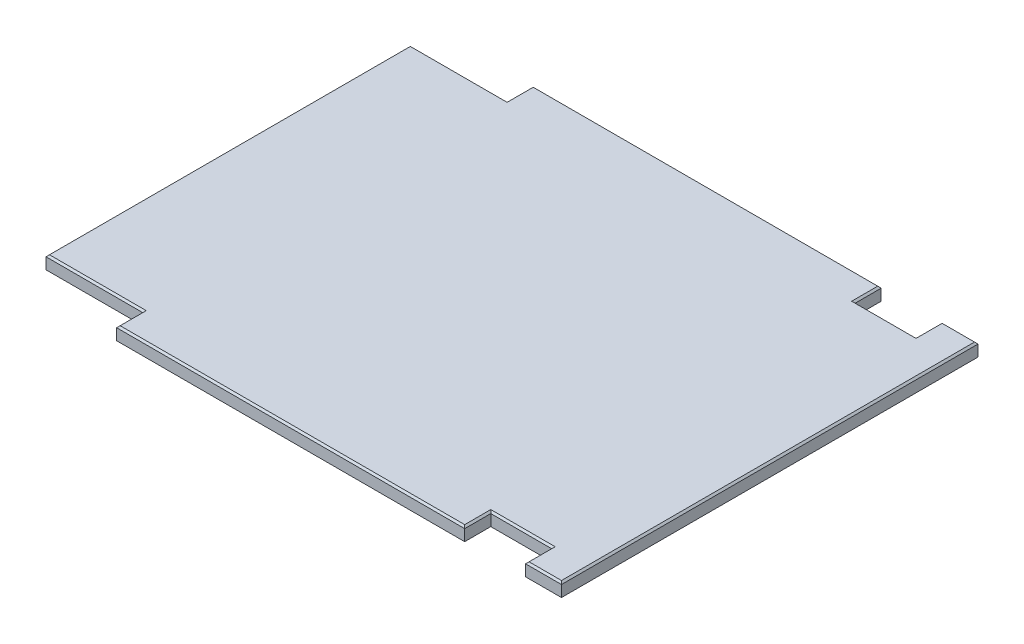
SolidWorks part; units mm, degrees
material "Oak"
ref_plane "Front Plane" through (0, 0, 0) normal (0, 0, 1) x (1, 0, 0)
ref_plane "Top Plane" through (0, 0, 0) normal (0, 1, 0) x (1, 0, 0)
ref_plane "Right Plane" through (0, 0, 0) normal (1, 0, 0) x (0, 0, -1)
sketch "Sketch1" plane through (0, 0, 0) normal (0, 1, 0) x (1, 0, 0)
  line L1 (0, 0) -> (790.575, 0)
  line L2 (0, 0) -> (0, 608.0125)
  line L3 (0, 608.0125) -> (790.575, 608.0125)
  line L4 (790.575, 0) -> (790.575, 608.0125)
  dimension "D1" = 608.0125
  dimension "D2" = 790.575
extrude "Boss-Extrude1" add sketch "Sketch1" along normal blind 19.05
sketch "Sketch2" plane through (0, 19.05, 0) normal (0, 1, 0) x (1, 0, 0)
  line L0 (-127.9594, 304.0062) -> (1156.0653, 304.0062) construction
  line L1 (738.1875, 569.9125) -> (649.2875, 569.9125)
  line L2 (738.1875, 569.9125) -> (738.1875, 608.0125)
  line L3 (738.1875, 608.0125) -> (649.2875, 608.0125)
  line L4 (649.2875, 569.9125) -> (649.2875, 608.0125)
  line L5 (0, 0) -> (790.575, 0) construction
  line L6 (0, 608.0125) -> (141.2875, 608.0125)
  line L7 (0, 608.0125) -> (0, 569.9125)
  line L8 (0, 569.9125) -> (141.2875, 569.9125)
  line L9 (141.2875, 608.0125) -> (141.2875, 569.9125)
  line L10 (0, 608.0125) -> (0, 0) construction
  line L11 (141.2875, 0) -> (141.2875, 38.1)
  line L12 (790.575, 608.0125) -> (0, 608.0125) construction
  line L13 (0, 38.1) -> (141.2875, 38.1)
  line L14 (0, 0) -> (0, 38.1)
  line L15 (0, 0) -> (141.2875, 0)
  line L16 (649.2875, 38.1) -> (649.2875, 0)
  line L17 (738.1875, 0) -> (649.2875, 0)
  line L18 (738.1875, 38.1) -> (738.1875, 0)
  line L19 (738.1875, 38.1) -> (649.2875, 38.1)
  line L20 (395.2875, -95.8271) -> (395.2875, 666.2246) construction
  line L21 (790.575, 0) -> (790.575, 608.0125) construction
  point P28 (141.2875, 588.9625)
  point P29 (649.2875, 588.9625)
  dimension "D1" = 508
  dimension "D3" = 88.9
  dimension "D5" = 38.1
extrude "Cut-Extrude1" cut sketch "Sketch2" against normal through all
chamfer "Chamfer1" distance 2.54 angle 45 16 edges at (790.575, 19.05, -304.0062) (764.3813, 19.05, 0) (0, 19.05, -304.0062) (764.3813, 19.05, -608.0125) (395.2875, 19.05, -608.0125) (70.6437, 19.05, -569.9125) (141.2875, 19.05, -588.9625) (649.2875, 19.05, -588.9625) (693.7375, 19.05, -569.9125) (738.1875, 19.05, -588.9625) (649.2875, 19.05, -19.05) (395.2875, 19.05, 0) (141.2875, 19.05, -19.05) (70.6437, 19.05, -38.1) (738.1875, 19.05, -19.05) (693.7375, 19.05, -38.1)
